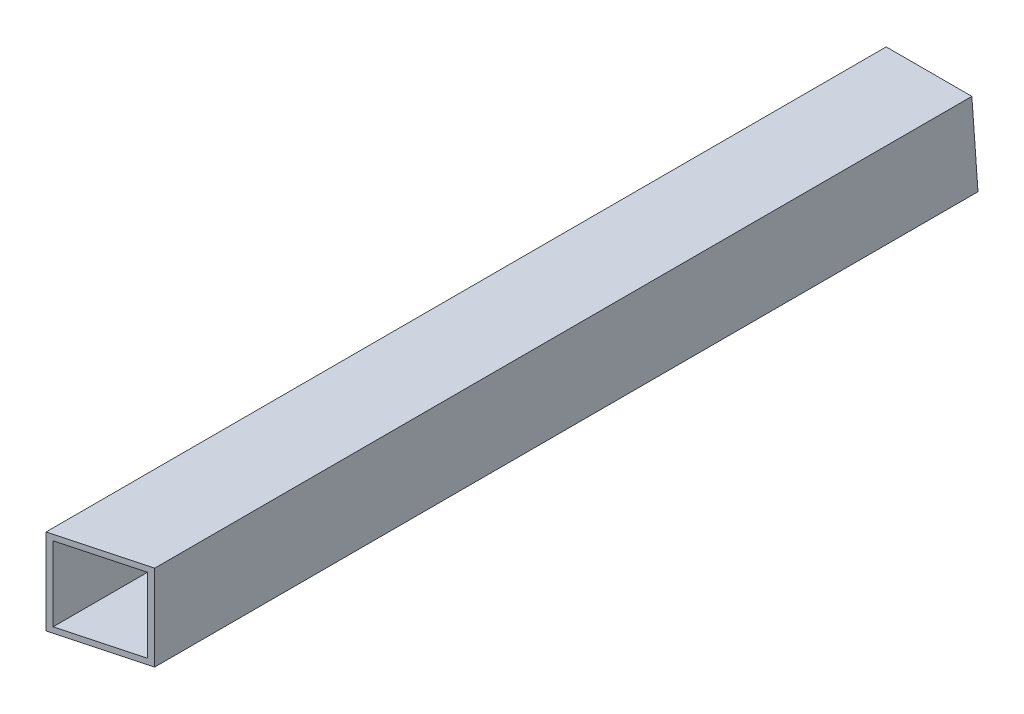
SolidWorks part; units mm, degrees
ref_plane "Front Plane" through (0, 0, 0) normal (0, 0, 1) x (1, 0, 0)
ref_plane "Top Plane" through (0, 0, 0) normal (0, 1, 0) x (1, 0, 0)
ref_plane "Right Plane" through (0, 0, 0) normal (1, 0, 0) x (0, 0, -1)
sketch "Sketch1" plane through (0, 0, 0) normal (0, 0, 1) x (1, 0, 0)
  line L1 (11.049, 11.049) -> (-11.049, 11.049)
  line L2 (11.049, 11.049) -> (11.049, -11.049)
  line L3 (11.049, -11.049) -> (-11.049, -11.049)
  line L4 (-11.049, 11.049) -> (-11.049, -11.049)
  line L5 (11.049, 11.049) -> (-11.049, -11.049) construction
  line L6 (11.049, -11.049) -> (-11.049, 11.049) construction
  line L7 (12.7, 12.7) -> (-12.7, 12.7)
  line L8 (12.7, 12.7) -> (12.7, -12.7)
  line L9 (12.7, -12.7) -> (-12.7, -12.7)
  line L10 (-12.7, 12.7) -> (-12.7, -12.7)
  line L11 (12.7, 12.7) -> (-12.7, -12.7) construction
  line L12 (12.7, -12.7) -> (-12.7, 12.7) construction
  point P0 (0, 0)
  point P6 (0, 0)
  dimension "D3" = 1.651
  dimension "D4" = 1.651
  dimension "D5" = 1.651
  dimension "D2" = 25.4
  dimension "D1" = 25.4
extrude "Boss-Extrude1" add sketch "Sketch1" against normal up to vertex (250 mm away)
sketch "Sketch3" plane through (0, 0, 0) normal (0, 1, 0) x (1, 0, 0)
  line L0 (0, 12.8662) -> (0, -262.1311) construction
  line L1 (0, -13.97) -> (0, 13.97) construction
ref_point "Point1"
sketch "Sketch5" plane through (0, 0, -250) normal (0, 0, -1) x (-1, 0, 0)
  line L0 (11.049, -11.049) -> (-11.049, -11.049) construction
  line L1 (-11.049, -11.049) -> (-11.049, 11.049) construction
  line L2 (-11.049, 11.049) -> (11.049, 11.049) construction
  line L3 (11.049, 11.049) -> (11.049, -11.049) construction
  line L4 (-12.7, 12.7) -> (12.7, 12.7) construction
  line L5 (12.7, 12.7) -> (12.7, -12.7) construction
  line L6 (12.7, -12.7) -> (-12.7, -12.7) construction
  line L7 (-12.7, -12.7) -> (-12.7, 12.7) construction
  line L8 (11.049, -11.049) -> (-11.049, -11.049)
  line L9 (-11.049, -11.049) -> (-11.049, 11.049)
  line L10 (-11.049, 11.049) -> (11.049, 11.049)
  line L11 (11.049, 11.049) -> (11.049, -11.049)
  line L12 (-12.7, 12.7) -> (12.7, 12.7)
  line L13 (12.7, 12.7) -> (12.7, -12.7)
  line L14 (12.7, -12.7) -> (-12.7, -12.7)
  line L15 (-12.7, -12.7) -> (-12.7, 12.7)
extrude "Boss-Extrude2" add sketch "Sketch5" along normal blind 25.4
sketch "Sketch6" plane through (-151.3216, -359.3194, -111.9717) normal (1, 0, 0) x (0, 0, 1)
  line L0 (-136.2109, -384.7041) -> (-139.8457, -333.9346)
  line L1 (-139.8457, -333.9346) -> (-118.0283, -359.3194) construction
  line L2 (-138.0283, -359.3194) -> (111.9717, -359.3194) construction
  line L3 (-139.8457, -333.9346) -> (-157.8243, -362.1685) construction
  line L4 (-125.2934, -357.4865) -> (-397.4859, -396.6616) construction
  line L5 (-139.8457, -333.9346) -> (-224.9548, -363.3401)
  line L6 (-224.9548, -363.3401) -> (-136.2109, -384.7041)
  dimension "D1" = 20
  dimension "D2" = 20
extrude "Cut-Extrude1" cut sketch "Sketch6" along normal through all
sketch "Sketch7" plane through (0, -12.7, 0) normal (0, -1, 0) x (1, 0, 0)
  line L0 (-12.7, 0) -> (24.6452, -10.0066)
  line L1 (24.6452, -10.0066) -> (24.6452, 0)
  line L2 (137.5, 0) -> (-137.5, 0) construction
  line L3 (24.6452, 0) -> (-12.7, 0)
  dimension "D1" = 15
extrude "Cut-Extrude2" cut sketch "Sketch7" against normal through all
equation "\"c1c2Len\"= 250"
equation "\"1inchSquareTubeLen\"=25.4"
equation "\"D2@Sketch1\"=\"1inchSquareTubeLen\""
equation "\"D1@Sketch1\"=\"1inchSquareTubeLen\""
equation "\"squareTubeWallThickness\"=1.651"
equation "\"D5@Sketch1\"=\"squareTubeWallThickness\""
equation "\"D4@Sketch1\"=\"squareTubeWallThickness\""
equation "\"D3@Sketch1\"=\"squareTubeWallThickness\""
